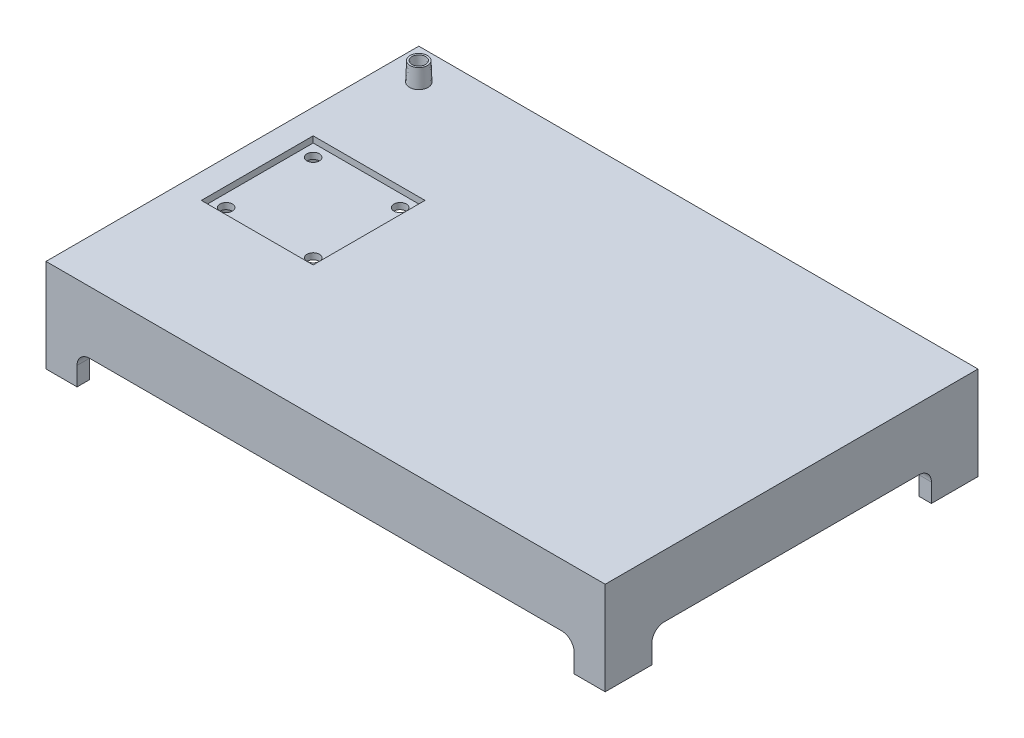
SolidWorks part; units mm, degrees
ref_plane "Front Plane" through (0, 0, 0) normal (0, 0, 1) x (1, 0, 0)
ref_plane "Top Plane" through (0, 0, 0) normal (0, 1, 0) x (1, 0, 0)
ref_plane "Right Plane" through (0, 0, 0) normal (1, 0, 0) x (0, 0, -1)
sketch "Sketch1" plane through (0, 0, 0) normal (0, 1, 0) x (1, 0, 0)
  line L1 (-225, -150) -> (225, -150)
  line L2 (-225, -150) -> (-225, 150)
  line L3 (-225, 150) -> (225, 150)
  line L4 (225, -150) -> (225, 150)
  line L5 (-225, -150) -> (225, 150) construction
  line L6 (-225, 150) -> (225, -150) construction
  point P0 (0, 0)
  dimension "D1" = 450
  dimension "D2" = 300
extrude "Boss-Extrude1" add sketch "Sketch1" along normal blind 75
shell "Shell1" thickness 10
sketch "Sketch2" plane through (225, 0, 0) normal (1, 0, 0) x (0, 0, -1)
  line L1 (-102.5, 25) -> (102.5, 25)
  line L2 (-112.5, 15) -> (-112.5, -15)
  line L3 (-102.5, -25) -> (102.5, -25)
  line L4 (112.5, 15) -> (112.5, -15)
  line L5 (-112.5, 25) -> (112.5, -25) construction
  line L6 (-112.5, -25) -> (112.5, 25) construction
  arc A0 (102.5, 25) -> (112.5, 15) centre (102.5, 15) cw
  arc A1 (-112.5, -15) -> (-102.5, -25) centre (-102.5, -15) ccw
  arc A2 (-102.5, 25) -> (-112.5, 15) centre (-102.5, 15) ccw
  arc A3 (102.5, -25) -> (112.5, -15) centre (102.5, -15) ccw
  point P0 (0, 0)
  dimension "D3" = 10
  dimension "D1" = 225
  dimension "D2" = 50
extrude "Cut-Extrude1" cut sketch "Sketch2" against normal through all
sketch "Sketch3" plane through (0, 0, 150) normal (0, 0, 1) x (1, 0, 0)
  line L1 (-190, -25) -> (190, -25)
  line L2 (-200, -15) -> (-200, 15)
  line L3 (-190, 25) -> (190, 25)
  line L4 (200, -15) -> (200, 15)
  line L5 (-200, -25) -> (200, 25) construction
  line L6 (-200, 25) -> (200, -25) construction
  arc A0 (-200, -15) -> (-190, -25) centre (-190, -15) ccw
  arc A1 (200, -15) -> (190, -25) centre (190, -15) cw
  arc A2 (200, 15) -> (190, 25) centre (190, 15) ccw
  arc A3 (-190, 25) -> (-200, 15) centre (-190, 15) ccw
  point P0 (0, 0)
  dimension "D3" = 10
  dimension "D1" = 400
  dimension "D2" = 50
extrude "Cut-Extrude2" cut sketch "Sketch3" against normal through all
sketch "Sketch4" plane through (0, 75, 0) normal (0, 1, 0) x (1, 0, 0)
  line L0 (225, 150) -> (-225, 150) construction
  circle A0 centre (-200, 125) radius 7.5
  circle A1 centre (-200, 125) radius 5
  dimension "D1" = 15
  dimension "D4" = 10
  dimension "D2" = 25
  dimension "D3" = 25
extrude "Boss-Extrude2" add sketch "Sketch4" along normal blind 15 draft 2
sketch "Sketch5" plane through (0, 75, 0) normal (0, 1, 0) x (1, 0, 0)
  circle A1 centre (-200, 125) radius 5.5238
  circle A2 centre (-200, 125) radius 5.5238
  dimension "D1" = 0
extrude "Cut-Extrude3" cut sketch "Sketch5" against normal blind 15
sketch "Sketch6" plane through (0, 75, 0) normal (0, 1, 0) x (1, 0, 0)
  line L1 (225, -150) -> (225, 150) construction
  line L2 (135, 80) -> (0, 80)
  line L3 (0, 80) -> (0, 105)
  line L4 (0, 105) -> (-65, 105)
  line L5 (-65, 105) -> (-65, 25)
  line L6 (-105, 120) -> (175, 120)
  line L9 (-105, 120) -> (-105, -120)
  line L10 (-105, -120) -> (175, -120)
  line L11 (175, 120) -> (175, 37.5)
  line L13 (0, 0) -> (320.3375, 0) construction
  line L14 (-65, 25) -> (0, 25)
  line L15 (0, 25) -> (0, 50)
  line L16 (0, 50) -> (135, 50)
  line L17 (135, 50) -> (135, 80)
  line L18 (135, -50) -> (135, -80)
  line L19 (0, -50) -> (135, -50)
  line L20 (0, -25) -> (0, -50)
  line L21 (-65, -25) -> (0, -25)
  line L22 (-65, -105) -> (-65, -25)
  line L23 (0, -105) -> (-65, -105)
  line L24 (0, -80) -> (0, -105)
  line L25 (135, -80) -> (0, -80)
  line L26 (175, -37.5) -> (175, -120)
  arc A0 (175, 37.5) -> (175, -37.5) centre (175, 0) ccw
  dimension "D10" = 75
  dimension "D1" = 40
  dimension "D2" = 280
  dimension "D3" = 50
  dimension "D4" = 240
  dimension "D5" = 30
  dimension "D6" = 25
  dimension "D7" = 25
  dimension "D8" = 15
  dimension "D9" = 40
extrude "Boss-Extrude3" add sketch "Sketch6" along normal blind 15
sketch "Sketch8" plane through (0, 75, 0) normal (0, 1, 0) x (1, 0, 0)
  line L0 (-105, 120) -> (-105, -120) construction
  line L1 (-205, -45) -> (-115, -45)
  line L2 (-205, -45) -> (-205, 45)
  line L3 (-205, 45) -> (-115, 45)
  line L4 (-115, -45) -> (-115, 45)
  line L5 (-205, -45) -> (-115, 45) construction
  line L6 (-205, 45) -> (-115, -45) construction
  point P0 (-160, 0)
  dimension "D1" = 90
  dimension "D2" = 90
  dimension "D3" = 10
extrude "Cut-Extrude5" cut sketch "Sketch8" against normal blind 5
sketch "Sketch9" plane through (0, 70, 0) normal (0, 1, 0) x (1, 0, 0)
  line L1 (-115, 45) -> (-205, 45) construction
  line L2 (-205, 45) -> (-205, -45) construction
  line L3 (-115, -45) -> (-115, 45) construction
  line L4 (-205, -45) -> (-115, -45) construction
  line L5 (-195, -35) -> (-125, 35) construction
  line L6 (-195, 35) -> (-125, -35) construction
  circle A0 centre (-195, 35) radius 5
  circle A1 centre (-125, 35) radius 5
  circle A2 centre (-125, -35) radius 5
  circle A3 centre (-195, -35) radius 5
  point P0 (-160, 0)
  dimension "D4" = 10
  dimension "D1" = 70
  dimension "D2" = 70
  dimension "D3" = 10
  dimension "D5" = 10
  dimension "D6" = 10
  dimension "D7" = 10
  dimension "D8" = 10
extrude "Cut-Extrude6" cut sketch "Sketch9" against normal blind 65
sketch "Sketch11" plane through (0, 0, 120) normal (0, 0, 1) x (1, 0, 0)
  line L1 (-105, 75) -> (175, 75)
  line L2 (-105, 75) -> (-105, 90)
  line L3 (-105, 90) -> (175, 90)
  line L4 (175, 75) -> (175, 90)
extrude "Cut-Extrude8" cut sketch "Sketch11" against normal through all
